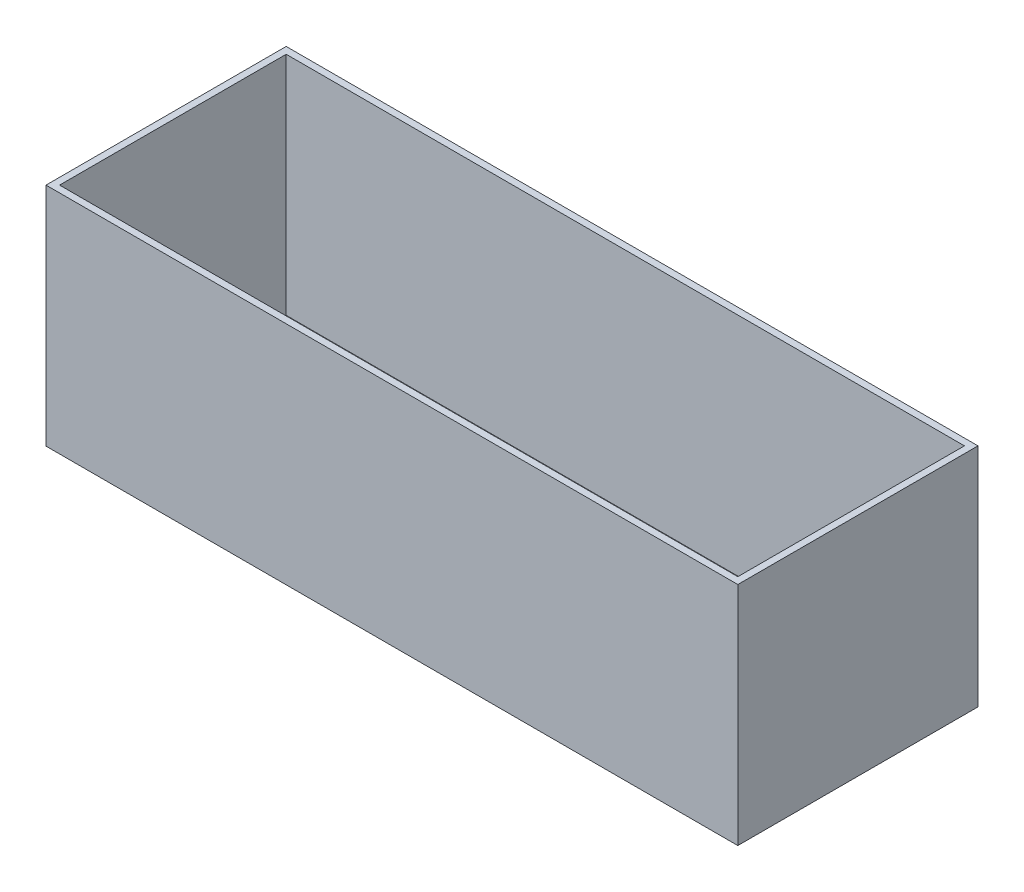
SolidWorks part; units mm, degrees
ref_plane "Front Plane" through (0, 0, 0) normal (0, 0, 1) x (1, 0, 0)
ref_plane "Top Plane" through (0, 0, 0) normal (0, 1, 0) x (1, 0, 0)
ref_plane "Right Plane" through (0, 0, 0) normal (1, 0, 0) x (0, 0, -1)
sketch "Sketch2" plane through (0, 0, 0) normal (0, 1, 0) x (1, 0, 0)
  line L0 (0, 0) -> (0, 100.24)
  line L1 (0, 100.24) -> (300, 100.24)
  line L2 (300, 100.24) -> (300, 0)
  line L3 (300, 0) -> (0, 0)
  line L4 (-3, 103.24) -> (303, 103.24)
  line L5 (303, 103.24) -> (303, -3)
  line L6 (303, -3) -> (-3, -3)
  line L7 (-3, -3) -> (-3, 103.24)
  dimension "D1" = 100.24
  dimension "D2" = 300
  dimension "D3" = 3
extrude "Boss-Extrude1" add sketch "Sketch2" along normal blind 100
